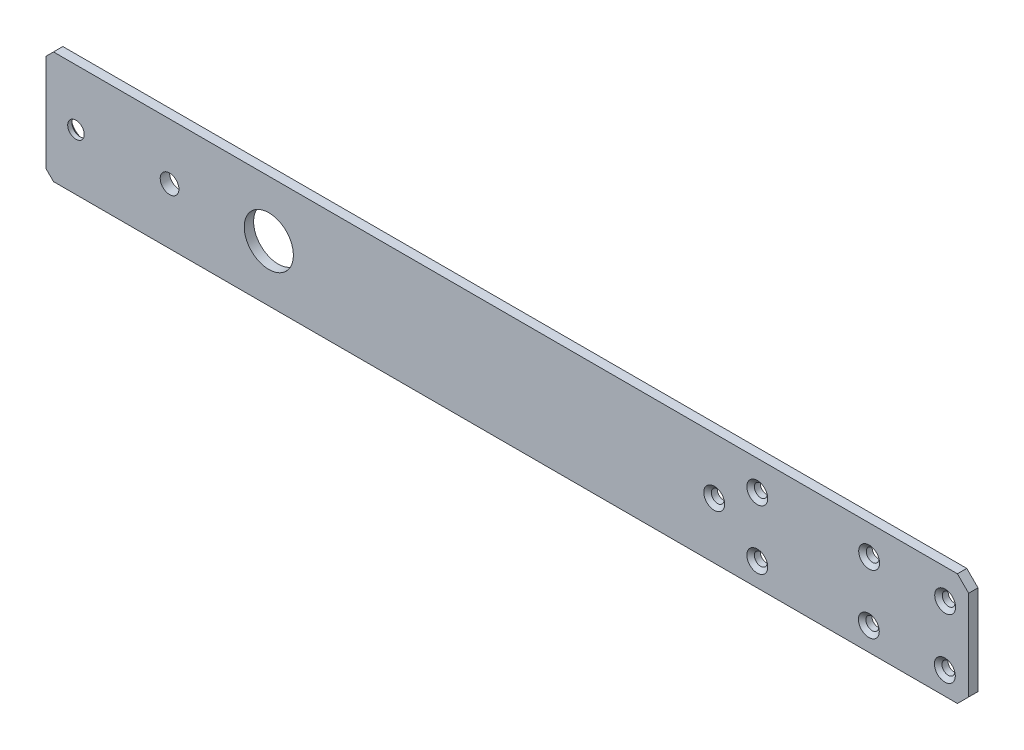
SolidWorks part; units mm, degrees
material "6061-T6 (SS)"
ref_plane "Front Plane" through (0, 0, 0) normal (0, 0, 1) x (1, 0, 0)
ref_plane "Top Plane" through (0, 0, 0) normal (0, 1, 0) x (1, 0, 0)
ref_plane "Right Plane" through (0, 0, 0) normal (1, 0, 0) x (0, 0, -1)
sketch "Sketch1" plane through (0, 0, 0) normal (0, 0, 1) x (1, 0, 0)
  line L0 (0, 19.05) -> (-28.575, 19.05)
  line L1 (0, -19.05) -> (247.2819, -19.05)
  line L2 (0, -19.05) -> (0, 19.05) construction
  line L3 (0, 19.05) -> (254, 19.05)
  line L5 (-28.575, 19.05) -> (-28.575, -19.05)
  line L6 (-28.575, -19.05) -> (0, -19.05)
  line L8 (254, 19.05) -> (247.2819, -19.05)
  circle A1 centre (0, 0) radius 8.3344
  dimension "D3" = 16.6687
  dimension "D1" = 38.1
  dimension "D2" = 254
  dimension "D4" = 80
extrude "Boss-Extrude1" add sketch "Sketch1" along normal mid plane 3.175
hole_wizard "#6 Clearance Hole3" positions "Sketch8" profile "Sketch7" hole size "#6" standard "ANSI Inch" end condition through all
sketch "Sketch8" plane through (0, 0, 1.5875) normal (0, 0, 1) x (1, 0, 0)
  point P0 (229.3887, 8.9238)
  point P3 (229.2824, -11.3468)
  point P6 (203.5032, -11.1439)
  point P9 (203.6088, 8.9914)
  point P12 (165.6722, 8.9914)
  point P15 (165.6722, -11.1439)
  point P18 (151.0672, 0)
sketch "Sketch7" plane through (229.3887, 8.9238, 1.5875) normal (1, 0, 0) x (0, -1, 0)
  line L0 (0, 0) -> (0, 3.175)
  line L1 (0, 3.175) -> (2.1526, 3.175)
  line L2 (2.1526, 3.175) -> (2.1526, 0)
  line L5 (2.1526, 0) -> (0, 0)
  line L11 (0, -6.35) -> (0, 107.95) construction
  dimension "Thru Hole Dia." = 4.3053
  dimension "Thru Hole Depth" = 3.175
sketch "Sketch9" plane through (0, 0, 1.5875) normal (0, 0, 1) x (1, 0, 0)
  line L0 (254, 19.05) -> (247.2819, -19.05)
  line L1 (254, 19.05) -> (237.3521, 19.05)
  line L2 (254, 19.05) -> (-28.575, 19.05) construction
  line L3 (237.3521, 19.05) -> (237.3521, -19.05)
  line L4 (-28.575, -19.05) -> (247.2819, -19.05) construction
  line L5 (237.3521, -19.05) -> (247.2819, -19.05)
  line L6 (243.8073, 17.5595) -> (237.0893, -20.5405) construction
extrude "Cut-Extrude1" cut sketch "Sketch9" against normal through all
chamfer "Chamfer1" distance 3.81 angle 45 4 edges at (-28.575, -19.05, 0) (-28.575, 19.05, 0) (237.3521, 19.05, 0) (237.3521, -19.05, 0)
hole_wizard "CSK for #6 Flat Head Machine Screw (100)2" positions "Sketch12" profile "Sketch13" countersink size "#6" standard "ANSI Inch" end condition through all
sketch "Sketch12" plane through (0, 0, 1.5875) normal (0, 0, 1) x (1, 0, 0)
  point P0 (203.6088, 8.9914)
  point P3 (203.5032, -11.1439)
  point P6 (229.2824, -11.3468)
  point P9 (229.3887, 8.9238)
  point P12 (165.6722, 8.9914)
  point P15 (165.6722, -11.1439)
  point P18 (151.0672, 0)
sketch "Sketch13" plane through (203.6088, 8.9914, 1.5875) normal (1, 0, 0) x (0, -1, 0)
  line L0 (0, 0) -> (0, 3.175)
  line L1 (0, 3.175) -> (2.1526, 3.175)
  line L2 (2.1526, 3.175) -> (2.1526, 1.1669)
  line L3 (2.1526, 1.1669) -> (3.5433, 0)
  line L5 (3.5433, 0) -> (0, 0)
  line L6 (-2.1526, 1.1669) -> (-3.5433, 0) construction
  line L11 (0, -6.35) -> (0, 107.95) construction
  dimension "Thru Hole Dia." = 4.3053
  dimension "Thru Hole Depth" = 3.175
  dimension "Near C'Sink Dia." = 7.0866
  dimension "Near C'Sink Angle" = 100
sketch "Sketch14" plane through (0, 0, 1.5875) normal (0, 0, 1) x (1, 0, 0)
  line L1 (-24.765, 19.05) -> (-75.565, 19.05)
  line L2 (-24.765, 19.05) -> (-24.765, -19.05)
  line L3 (-24.765, -19.05) -> (-75.565, -19.05)
  line L4 (-75.565, 19.05) -> (-75.565, -19.05)
  dimension "D1" = 50.8
extrude "Boss-Extrude2" add sketch "Sketch14" against normal through all
chamfer "Chamfer2" distance 2.54 angle 45 2 edges at (-75.565, 19.05, 0) (-75.565, -19.05, 0)
hole_wizard "CSK for #10 Flat Head Machine Screw (100)1" positions "Sketch15" profile "Sketch16" countersink size "#10" standard "ANSI Inch" end condition through all
sketch "Sketch15" plane through (0, 0, -1.5875) normal (0, 0, 1) x (1, 0, 0)
  line L0 (0, 0) -> (-75.565, 0) construction
  line L1 (-75.565, 16.51) -> (-75.565, -16.51) construction
  point P0 (-65.405, 0)
  dimension "D1" = 10.16
sketch "Sketch16" plane through (-65.405, 0, -1.5875) normal (1, 0, 0) x (0, 1, 0)
  line L0 (0, 0) -> (0, 3.175)
  line L1 (0, 3.175) -> (2.8067, 3.175)
  line L2 (2.8067, 3.175) -> (2.8067, 1.7477)
  line L3 (2.8067, 1.7477) -> (4.8895, 0)
  line L5 (4.8895, 0) -> (0, 0)
  line L6 (-2.8067, 1.7477) -> (-4.8895, 0) construction
  line L11 (0, -6.35) -> (0, 107.95) construction
  dimension "Thru Hole Dia." = 5.6134
  dimension "Thru Hole Depth" = 3.175
  dimension "Near C'Sink Dia." = 9.779
  dimension "Near C'Sink Angle" = 100
hole_wizard "1/4 (0.25) Diameter Hole1" positions "Sketch19" profile "Sketch20" hole size "1/4" standard "ANSI Inch" end condition through all
sketch "Sketch19" plane through (0, 0, -1.5875) normal (0, 0, -1) x (-1, 0, 0)
  line L0 (75.565, 0) -> (33.655, 0) construction
  line L1 (75.565, 16.51) -> (75.565, -16.51) construction
  circle A1 centre (65.405, 0) radius 4.8895 construction
  point P0 (33.655, 0)
  dimension "D1" = 31.75
sketch "Sketch20" plane through (-33.655, 0, -1.5875) normal (1, 0, 0) x (0, 1, 0)
  line L0 (0, 0) -> (0, 3.175)
  line L1 (0, 3.175) -> (3.175, 3.175)
  line L2 (3.175, 3.175) -> (3.175, 0)
  line L5 (3.175, 0) -> (0, 0)
  line L11 (0, -6.35) -> (0, 107.95) construction
  dimension "Thru Hole Dia." = 6.35
  dimension "Thru Hole Depth" = 3.175
